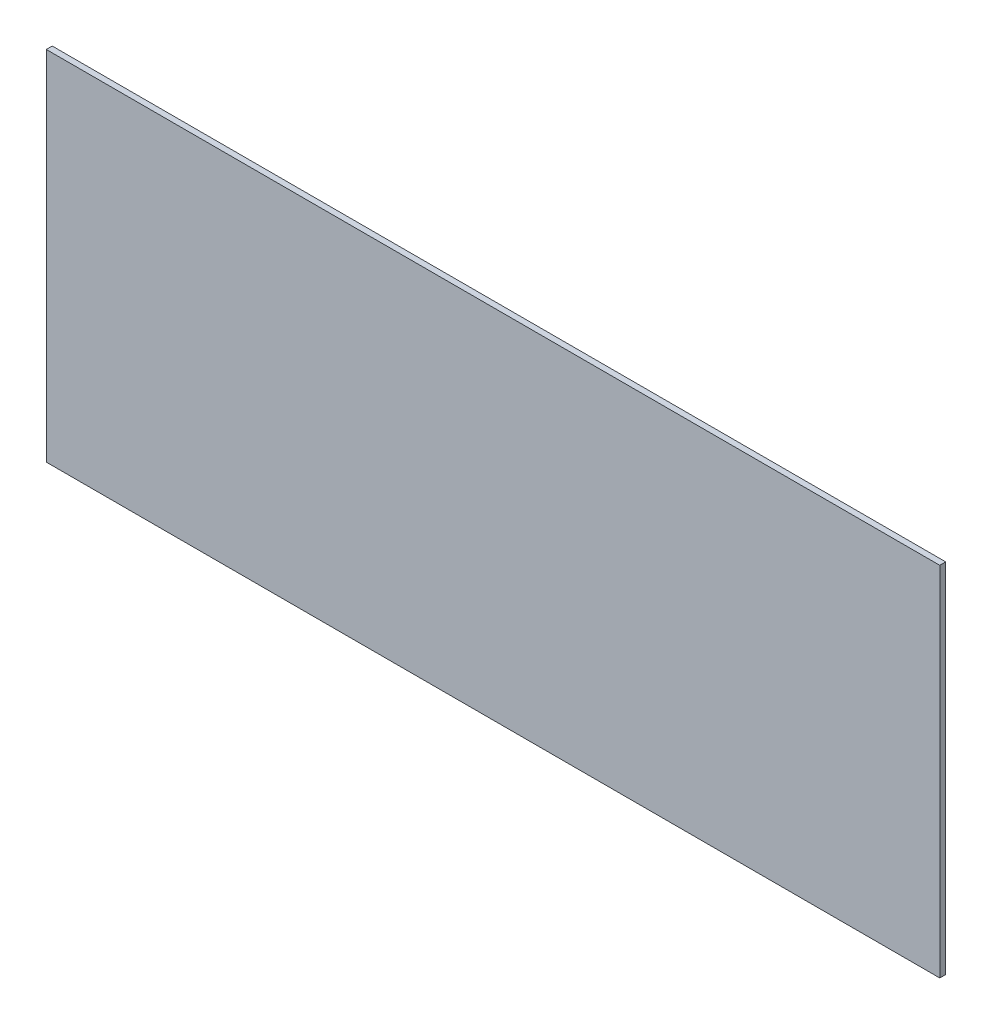
SolidWorks part; units mm, degrees
material "Acrylic (Medium-high impact)"
ref_plane "Front Plane" through (0, 0, 0) normal (0, 0, 1) x (1, 0, 0)
ref_plane "Top Plane" through (0, 0, 0) normal (0, 1, 0) x (1, 0, 0)
ref_plane "Right Plane" through (0, 0, 0) normal (1, 0, 0) x (0, 0, -1)
sketch "Sketch1" plane through (0, 0, 0) normal (0, 0, 1) x (1, 0, 0)
  line L1 (150, -36.7008) -> (-150, -36.7008)
  line L2 (150, -36.7008) -> (150, 83.2992)
  line L3 (150, 83.2992) -> (-150, 83.2992)
  line L4 (-150, -36.7008) -> (-150, 83.2992)
  line L5 (150, -36.7008) -> (-150, 83.2992) construction
  line L6 (150, 83.2992) -> (-150, -36.7008) construction
  point P0 (0, 23.2992)
  dimension "D1" = 300
  dimension "D2" = 120
extrude "Boss-Extrude1" add sketch "Sketch1" along normal blind 2
